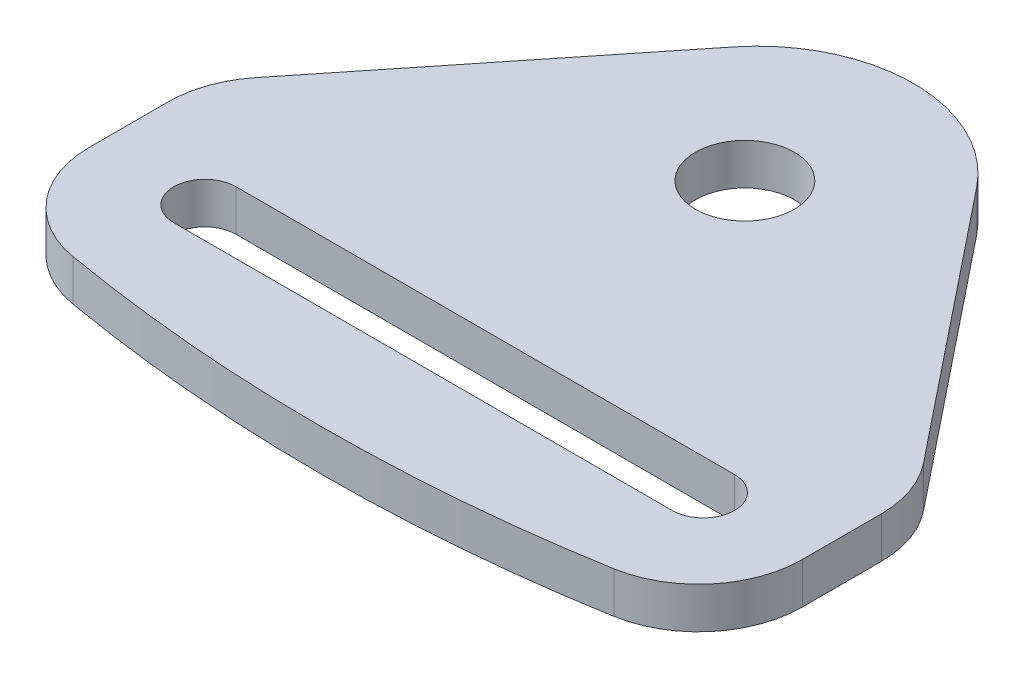
SolidWorks part; units mm, degrees
ref_plane "Front Plane" through (0, 0, 0) normal (0, 0, 1) x (1, 0, 0)
ref_plane "Top Plane" through (0, 0, 0) normal (0, 1, 0) x (1, 0, 0)
ref_plane "Right Plane" through (0, 0, 0) normal (1, 0, 0) x (0, 0, -1)
sketch "Sketch1" plane through (0, 0, 0) normal (0, 1, 0) x (1, 0, 0)
  line L1 (-58.35, 9) -> (-10.35, 9) construction
  line L2 (-58.35, 12) -> (-10.35, 12)
  line L3 (-58.35, 6) -> (-10.35, 6)
  line L4 (-68.7, 0) -> (-68.7, 19.3)
  line L5 (0, 0) -> (0, 19.3)
  line L6 (-68.7, 19.3) -> (-34.35, 62.2544)
  line L7 (-34.35, 62.2544) -> (0, 19.3)
  arc A0 (-68.7, 0) -> (0, 0) centre (-34.35, 149.0902) ccw
  arc A1 (-58.35, 12) -> (-58.35, 6) centre (-58.35, 9) ccw
  arc A2 (-10.35, 6) -> (-10.35, 12) centre (-10.35, 9) ccw
  circle A3 centre (-34.35, 37) radius 4.7625
  point P7 (-34.35, 9)
  dimension "D3" = 3
  dimension "D7" = 9.525
  dimension "D1" = 68.7
  dimension "D2" = 48
  dimension "D4" = 19.3
  dimension "D5" = 55
  dimension "D6" = 55
  dimension "D8" = 28
extrude "Boss-Extrude1" add sketch "Sketch1" along normal blind 3.9688
fillet "Fillet1" radius 10 4 edges at (0, 1.9844, -19.3) (-68.7, 1.9844, -19.3) (-68.7, 1.9844, 0) (0, 1.9844, 0)
fillet "Fillet2" radius 15 1 edges at (-34.35, 1.9844, -62.2544)
